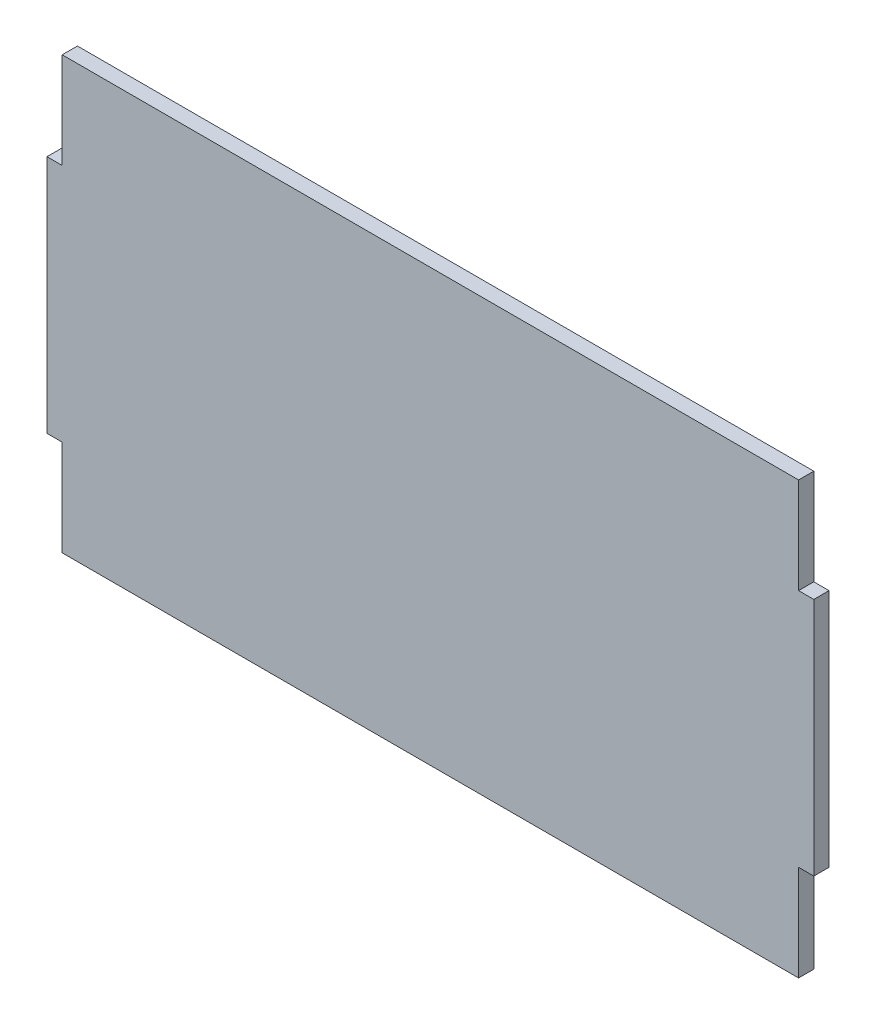
SolidWorks part; units mm, degrees
ref_plane "Front Plane" through (0, 0, 0) normal (0, 0, 1) x (1, 0, 0)
ref_plane "Top Plane" through (0, 0, 0) normal (0, 1, 0) x (1, 0, 0)
ref_plane "Right Plane" through (0, 0, 0) normal (1, 0, 0) x (0, 0, -1)
sketch "Sketch1" plane through (0, 0, 0) normal (0, 0, 1) x (1, 0, 0)
  line L0 (-2019.1373, 0) -> (1758.6941, 0) construction
  line L1 (0, 1235.915) -> (0, -1256.4281) construction
  line L2 (0, 0) -> (153.65, 0)
  line L3 (153.65, 0) -> (153.65, 20)
  line L4 (153.65, 20) -> (156.825, 20)
  line L5 (156.825, 20) -> (156.825, 70)
  line L6 (156.825, 70) -> (153.65, 70)
  line L7 (153.65, 70) -> (153.65, 90)
  line L8 (153.65, 90) -> (0, 90)
  line L9 (0, 90) -> (0, 70)
  line L10 (0, 70) -> (-3.175, 70)
  line L11 (-3.175, 70) -> (-3.175, 20)
  line L12 (-3.175, 20) -> (0, 20)
  line L13 (0, 20) -> (0, 0)
  dimension "D1" = 153.65
  dimension "D2" = 3.175
  dimension "D3" = 50
  dimension "D4" = 3.175
  dimension "D5" = 20
  dimension "D6" = 153.65
  dimension "D7" = 20
  dimension "D8" = 3.175
  dimension "D9" = 50
  dimension "D10" = 20
extrude "Boss-Extrude1" add sketch "Sketch1" along normal blind 3.175
